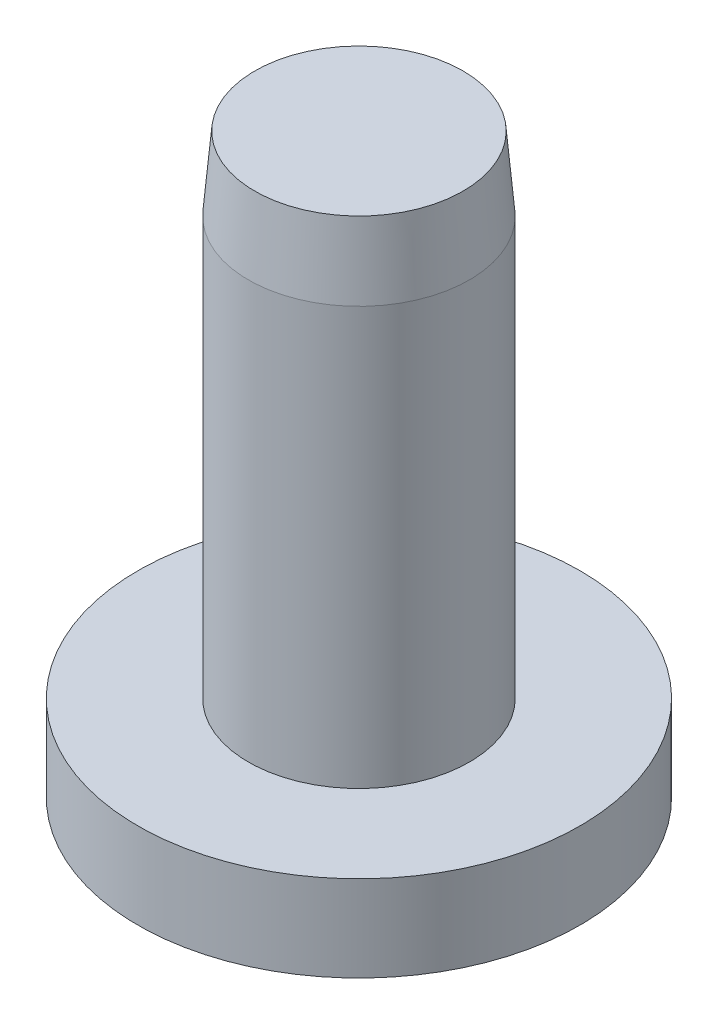
SolidWorks part; units mm, degrees
material "Литая легированная сталь"
ref_plane "Спереди" through (0, 0, 0) normal (0, 0, 1) x (1, 0, 0)
ref_plane "Сверху" through (0, 0, 0) normal (0, 1, 0) x (1, 0, 0)
ref_plane "Справа" through (0, 0, 0) normal (1, 0, 0) x (0, 0, -1)
sketch "Эскиз1" plane through (0, 0, 0) normal (0, 0, 1) x (1, 0, 0)
  line L0 (0, 0) -> (0, 21.5)
  line L1 (0, 21.5) -> (-4.5, 21.5)
  line L2 (-4.5, 21.5) -> (-4.5, 1.5)
  line L3 (-4.5, 1.5) -> (-9, 1.5)
  line L4 (-9, 1.5) -> (-9, -2)
  line L5 (-9, -2) -> (-8, -2)
  line L6 (-8, -2) -> (-8, 0)
  line L7 (-8, 0) -> (0, 0)
  dimension "D1" = 21.5
  dimension "D2" = 3.5
  dimension "D3" = 2
  dimension "D4" = 4.5
  dimension "D5" = 1
  dimension "D6" = 9
revolve "Повернуть1" add sketch "Эскиз1" angle 360 about L0
chamfer "Фаска1" distance 0.26 distance2 3 1 edges at (0, 21.5, -4.5)
